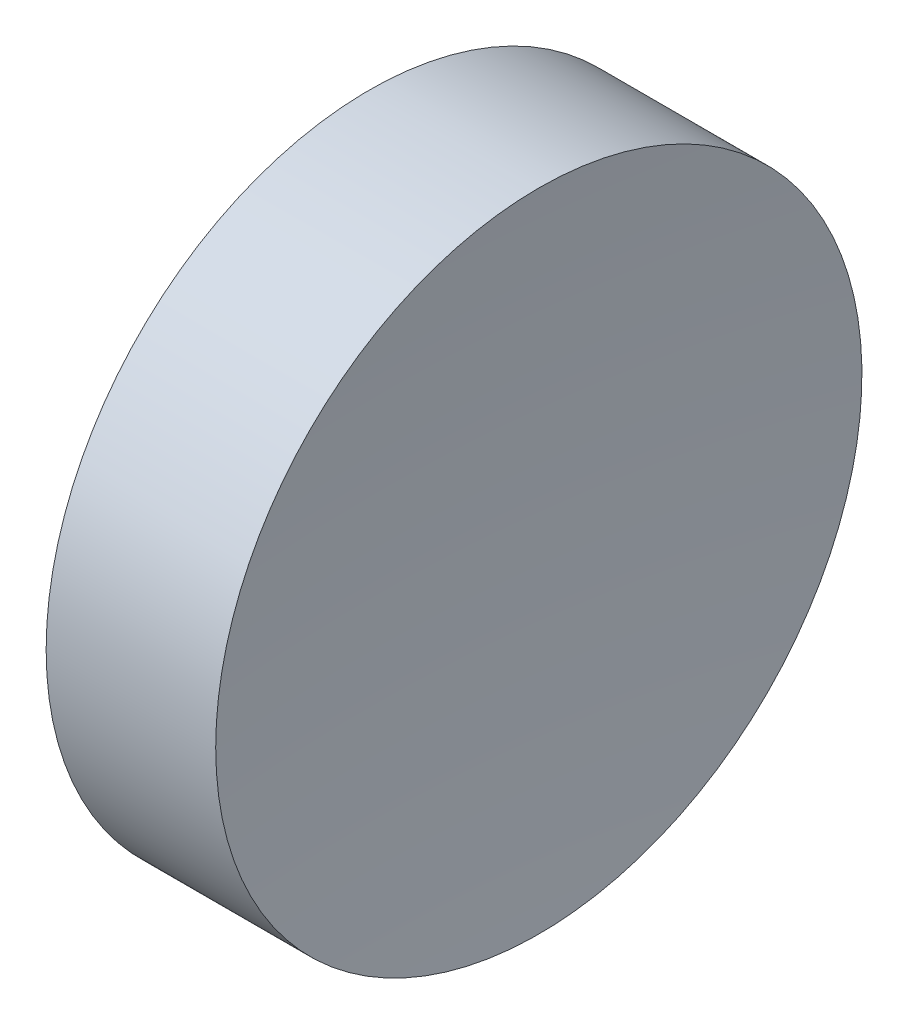
SolidWorks part; units mm, degrees
ref_plane "前视基准面" through (0, 0, 0) normal (0, 0, 1) x (1, 0, 0)
ref_plane "上视基准面" through (0, 0, 0) normal (0, 1, 0) x (1, 0, 0)
ref_plane "右视基准面" through (0, 0, 0) normal (1, 0, 0) x (0, 0, -1)
sketch "草图1" plane through (0, 0, 0) normal (0, 0, 1) x (1, 0, 0)
  line L0 (54.4926, 34.689) -> (66.3882, 34.689) construction
  line L1 (57.5463, 34.689) -> (57.5463, 40.939)
  line L2 (57.5463, 40.939) -> (60.8259, 40.939)
  line L3 (60.5463, 34.689) -> (57.5463, 34.689)
  arc A0 (60.8259, 40.939) -> (60.5463, 34.689) centre (130.5463, 34.689) ccw
  dimension "D1" = 3.2796
revolve "旋转1" add sketch "草图1" angle 360 about L0
